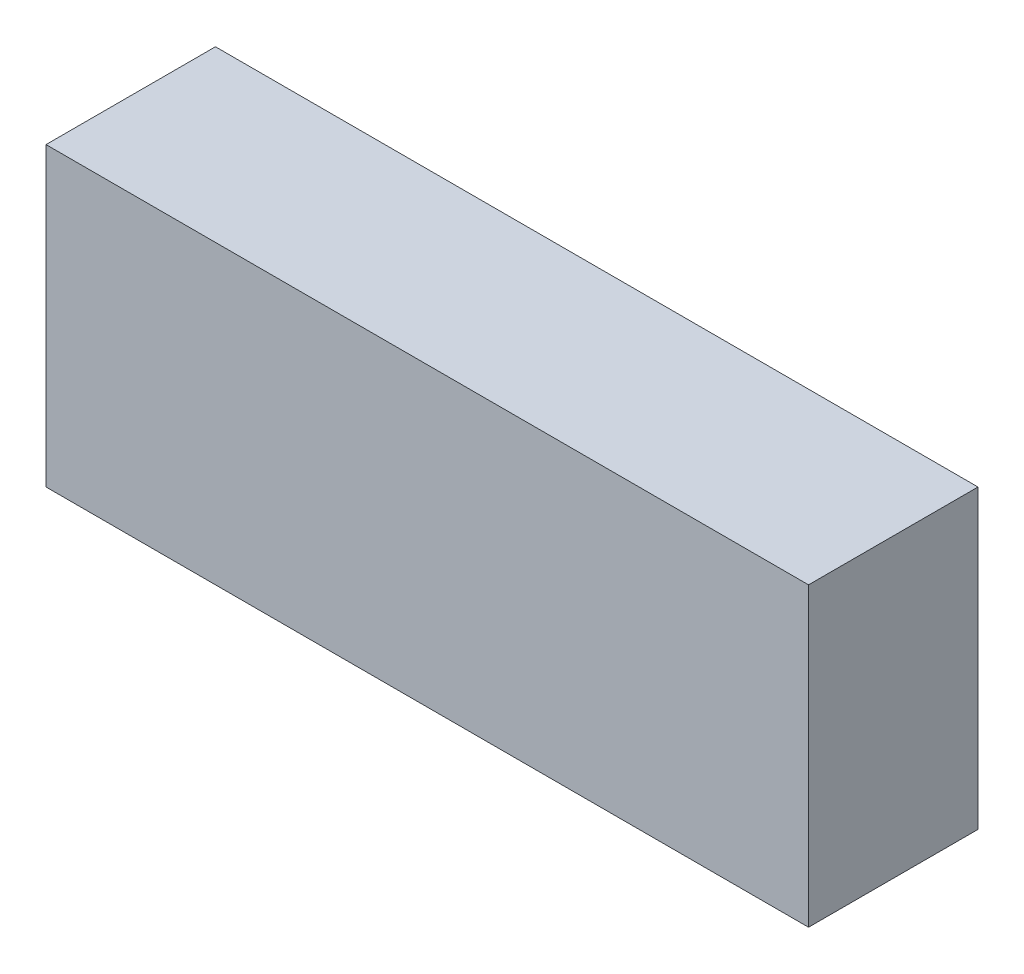
SolidWorks part; units mm, degrees
ref_plane "Plan de face" through (0, 0, 0) normal (0, 0, 1) x (1, 0, 0)
ref_plane "Plan de dessus" through (0, 0, 0) normal (0, 1, 0) x (1, 0, 0)
ref_plane "Plan de droite" through (0, 0, 0) normal (1, 0, 0) x (0, 0, -1)
sketch "Esquisse1" plane through (0, 0, 0) normal (0, 0, 1) x (1, 0, 0)
  line L1 (0, 0) -> (-90, 0)
  line L2 (0, 0) -> (0, 35)
  line L3 (0, 35) -> (-90, 35)
  line L4 (-90, 0) -> (-90, 35)
  dimension "D1" = 90
  dimension "D2" = 35
extrude "Boss.-Extru.1" add sketch "Esquisse1" along normal blind 20
